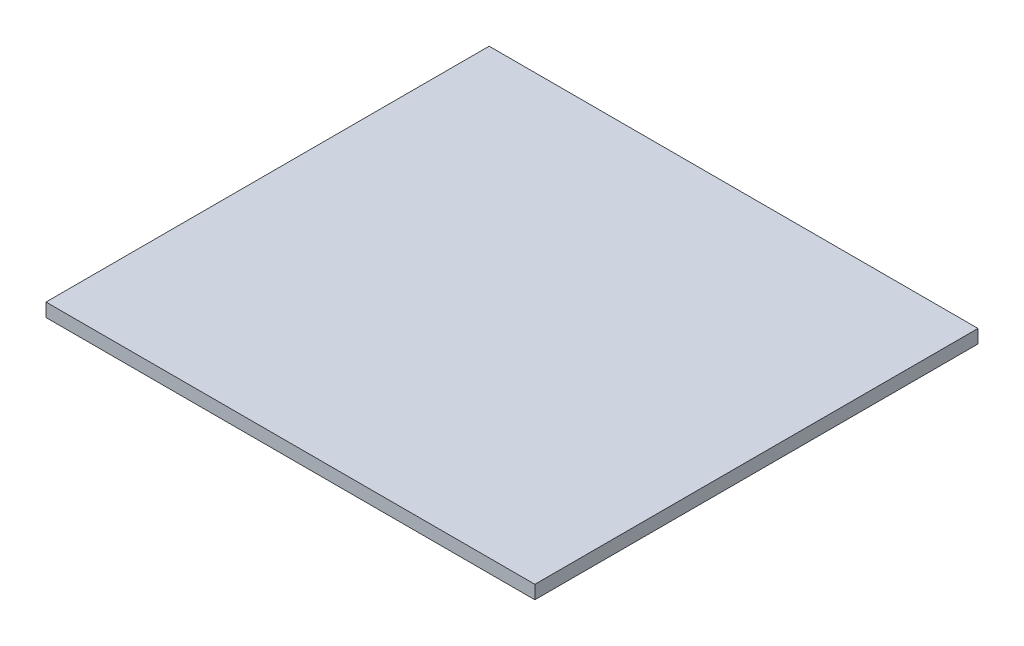
SolidWorks part; units mm, degrees
ref_plane "Front Plane" through (0, 0, 0) normal (0, 0, 1) x (1, 0, 0)
ref_plane "Top Plane" through (0, 0, 0) normal (0, 1, 0) x (1, 0, 0)
ref_plane "Right Plane" through (0, 0, 0) normal (1, 0, 0) x (0, 0, -1)
sketch "Sketch1" plane through (0, 0, 0) normal (0, 1, 0) x (1, 0, 0)
  line L1 (-44.2815, 20.698) -> (64.7185, 20.698)
  line L2 (-44.2815, 20.698) -> (-44.2815, -78.102)
  line L3 (-44.2815, -78.102) -> (64.7185, -78.102)
  line L4 (64.7185, 20.698) -> (64.7185, -78.102)
  dimension "D1" = 109
  dimension "D2" = 98.8
extrude "Boss-Extrude1" add sketch "Sketch1" along normal blind 3
equation "\"Fit\"= 1"
equation "\"cover width\"= 98.8"
equation "\"top 2-3-4-5 length\"= 109"
equation "\"thinner acrylic\"= 3"
equation "\"D1@Sketch1\"=\"top 2-3-4-5 length\""
equation "\"D2@Sketch1\"=\"cover width\""
equation "\"D1@Boss-Extrude1\"=\"thinner acrylic\""
